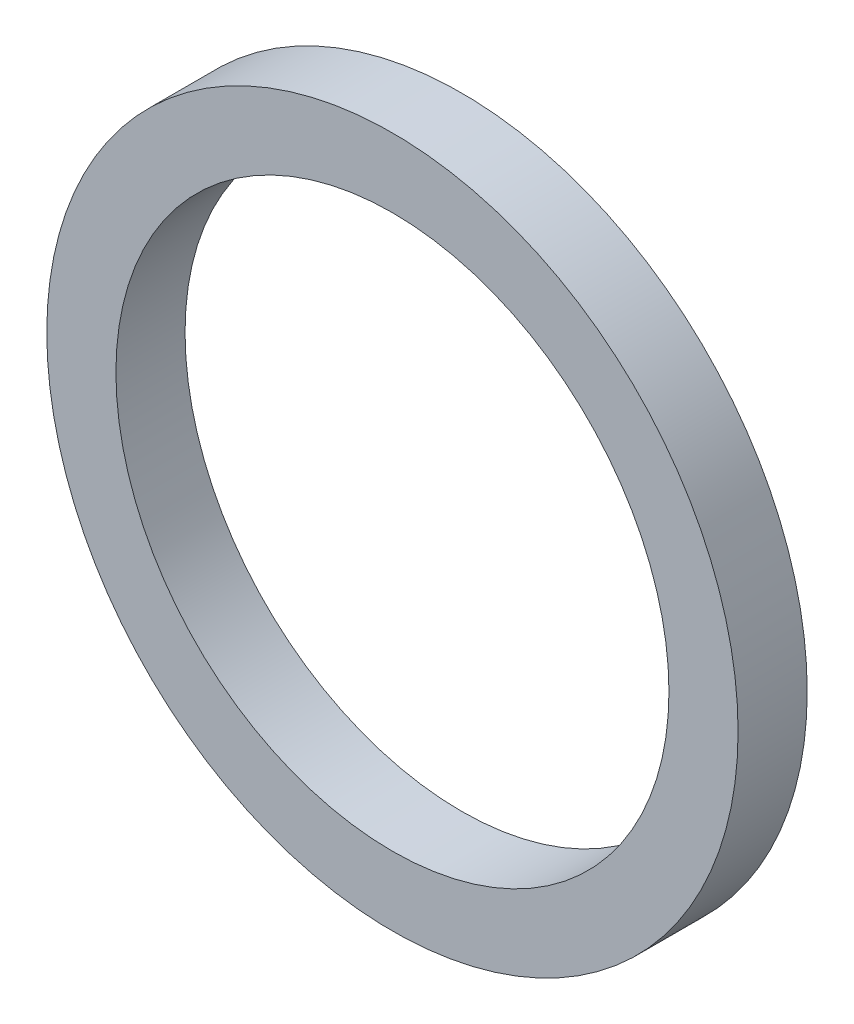
SolidWorks part; units mm, degrees
ref_plane "Płaszczyzna przednia" through (0, 0, 0) normal (0, 0, 1) x (1, 0, 0)
ref_plane "Płaszczyzna górna" through (0, 0, 0) normal (0, 1, 0) x (1, 0, 0)
ref_plane "Płaszczyzna prawa" through (0, 0, 0) normal (1, 0, 0) x (0, 0, -1)
sketch "Szkic1" plane through (0, 0, 0) normal (0, 0, 1) x (1, 0, 0)
  circle A0 centre (0, 0) radius 4
  circle A1 centre (0, 0) radius 5
  dimension "D1" = 8
  dimension "D2" = 10
extrude "Dodanie-wyciągnięcie1" add sketch "Szkic1" along normal blind 1
